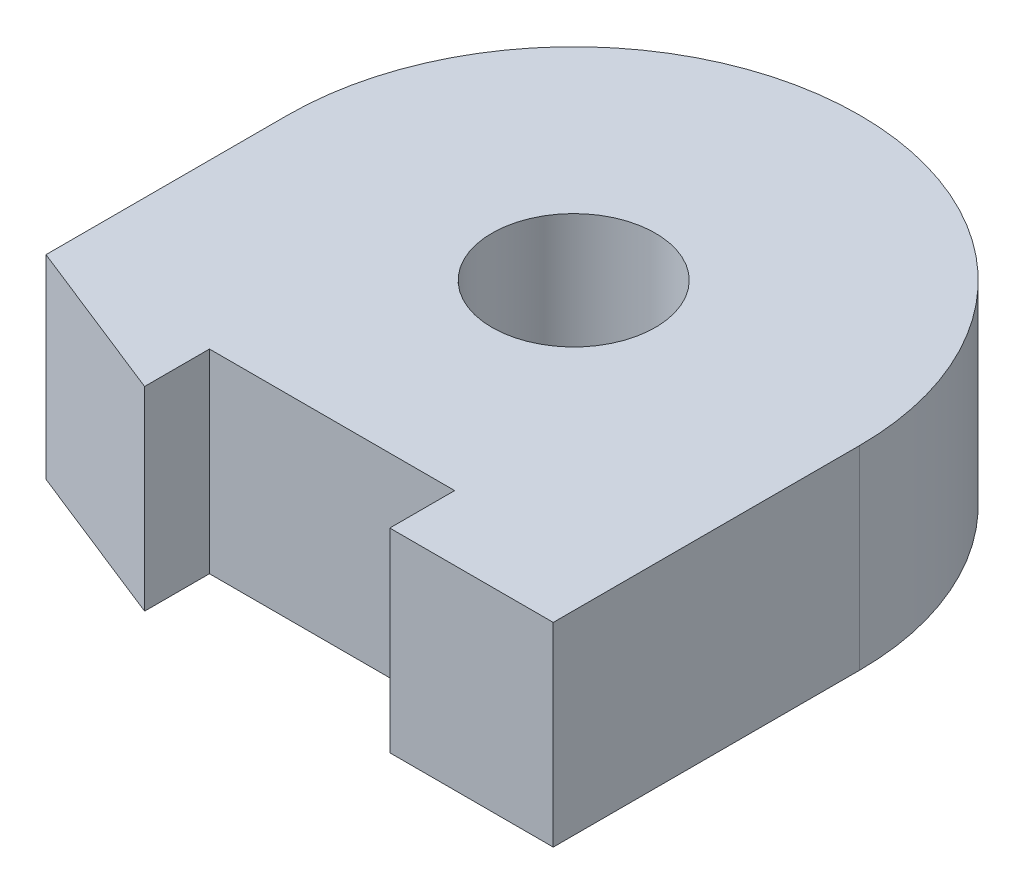
SolidWorks part; units mm, degrees
ref_plane "Front Plane" through (0, 0, 0) normal (0, 0, 1) x (1, 0, 0)
ref_plane "Top Plane" through (0, 0, 0) normal (0, 1, 0) x (1, 0, 0)
ref_plane "Right Plane" through (0, 0, 0) normal (1, 0, 0) x (0, 0, -1)
sketch "Sketch1" plane through (0, 0, 0) normal (0, 1, 0) x (1, 0, 0)
  line L0 (0, 0) -> (-6, 0)
  line L1 (-6, 0) -> (-6, -3.175)
  line L2 (-6, -3.175) -> (-14, -3.175)
  line L3 (-14, -3.175) -> (-14, 11.825)
  line L4 (0, 0) -> (6, 0)
  line L5 (6, 0) -> (6, -3.175)
  line L6 (6, -3.175) -> (14, -3.175)
  line L7 (14, -3.175) -> (14, 11.825)
  line L8 (-6, 0) -> (-14, 0) construction
  line L9 (-6, -3.175) -> (-14, 0)
  arc A0 (-14, 11.825) -> (14, 11.825) centre (0, 11.825) cw
  circle A1 centre (0, 11.825) radius 4
  dimension "D4" = 8
  dimension "D5" = 8
  dimension "D1" = 6
  dimension "D2" = 3.175
  dimension "D3" = 15
extrude "Boss-Extrude1" add sketch "Sketch1" along normal blind 9.525 contours L8 L0 L4 L5 L6 L7 A0 L3 A1 | L1 L8 L9
